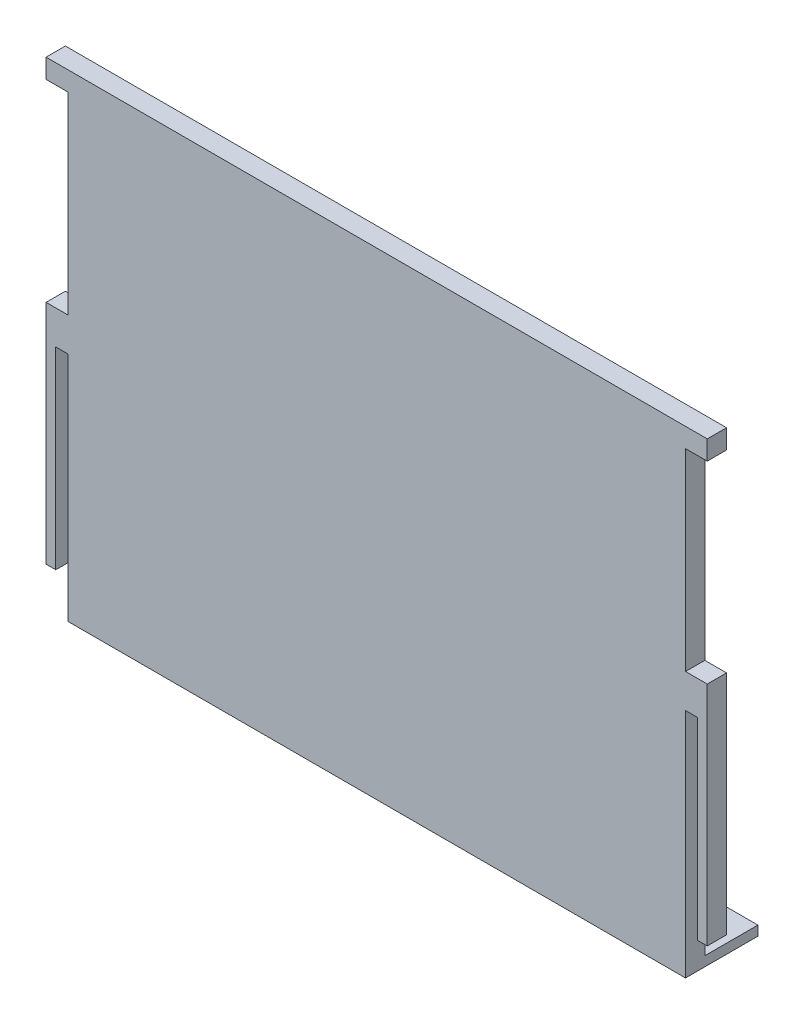
SolidWorks part; units mm, degrees
ref_plane "Front Plane" through (0, 0, 0) normal (0, 0, 1) x (1, 0, 0)
ref_plane "Top Plane" through (0, 0, 0) normal (0, 1, 0) x (1, 0, 0)
ref_plane "Right Plane" through (0, 0, 0) normal (1, 0, 0) x (0, 0, -1)
sketch "Sketch1" plane through (0, 0, 0) normal (0, 0, 1) x (1, 0, 0)
  line L1 (-68.5, -48) -> (68.5, -48)
  line L2 (-68.5, -48) -> (-68.5, 48)
  line L3 (-68.5, 48) -> (68.5, 48)
  line L4 (68.5, -48) -> (68.5, 48)
  line L5 (-68.5, -48) -> (68.5, 48) construction
  line L6 (-68.5, 48) -> (68.5, -48) construction
  point P0 (0, 0)
  dimension "D1" = 137
  dimension "D2" = 96
extrude "Boss-Extrude1" add sketch "Sketch1" along normal blind 4
sketch "Sketch2" plane through (0, 0, 4) normal (0, 0, 1) x (1, 0, 0)
  line L0 (-64, 66.1175) -> (-64, -52.561) construction
  line L1 (64, 66.1175) -> (64, -52.561) construction
  line L2 (-64, -40) -> (-64, 0)
  line L3 (64, 0) -> (64, -40)
  line L4 (-68.5, 48) -> (-68.5, -48) construction
  line L5 (-64, 0) -> (-66.5, 0)
  line L6 (-64, 0) -> (-64, -40)
  line L7 (-64, -40) -> (-66.5, -40)
  line L8 (-66.5, 0) -> (-66.5, -40)
  line L9 (64, 0) -> (66.5, 0)
  line L10 (64, 0) -> (64, -40)
  line L11 (64, -40) -> (66.5, -40)
  line L12 (66.5, 0) -> (66.5, -40)
  line L13 (-68.5, 47) -> (-64, 47)
  line L14 (-68.5, 47) -> (-68.5, 7)
  line L15 (-68.5, 7) -> (-64, 7)
  line L16 (-64, 47) -> (-64, 7)
  line L17 (68.5, -48) -> (68.5, 48) construction
  line L18 (64, 7) -> (68.5, 7)
  line L19 (64, 7) -> (64, 47)
  line L20 (64, 47) -> (68.5, 47)
  line L21 (68.5, 7) -> (68.5, 47)
  dimension "D1" = 128
  dimension "D2" = 64
  dimension "D3" = 40
  dimension "D4" = 2.5
  dimension "D5" = 2.5
  dimension "D6" = 8
  dimension "D7" = 7
  dimension "D8" = 40
extrude "Cut-Extrude1" cut sketch "Sketch2" against normal blind 4 contours L5 L8 L7 L2 | L12 L9 L3 L11 | L14 L15 L16 L13 | L21 L20 L19 L18
sketch "Sketch3" plane through (0, 48, 0) normal (0, 1, 0) x (1, 0, 0)
  line L1 (68.5, -4) -> (-68.5, -4)
  line L2 (68.5, -4) -> (68.5, 0)
  line L3 (68.5, 0) -> (-68.5, 0)
  line L4 (-68.5, -4) -> (-68.5, 0)
extrude "Boss-Extrude2" add sketch "Sketch3" along normal blind 3
sketch "Sketch4" plane through (0, 0, 0) normal (0, 0, -1) x (-1, 0, 0)
  line L0 (68.5, 7) -> (68.5, -48) construction
  line L1 (-68.5, -48) -> (68.5, -48)
  line L2 (-68.5, -48) -> (-68.5, -46)
  line L3 (-68.5, -46) -> (68.5, -46)
  line L4 (68.5, -48) -> (68.5, -46)
  dimension "D1" = 2
extrude "Boss-Extrude3" add sketch "Sketch4" along normal blind 11
sketch "Sketch5" plane through (0, 0, 4) normal (0, 0, 1) x (1, 0, 0)
  line L1 (-64, -40) -> (-68.5, -40)
  line L2 (-64, -40) -> (-64, -48)
  line L3 (-64, -48) -> (-68.5, -48)
  line L4 (-68.5, -40) -> (-68.5, -48)
  line L5 (64, -40) -> (68.5, -40)
  line L6 (64, -40) -> (64, -48)
  line L7 (64, -48) -> (68.5, -48)
  line L8 (68.5, -40) -> (68.5, -48)
extrude "Cut-Extrude2" cut sketch "Sketch5" against normal through all
sketch "Sketch6" plane through (0, 0, 0) normal (0, 0, -1) x (-1, 0, 0)
  line L0 (-20.8, -44.3) -> (-60, -44.3)
  line L1 (60, -44.3) -> (20.8, -44.3)
  line L2 (60, -44.3) -> (60, -16.1)
  line L3 (60, -16.1) -> (20.8, -16.1)
  line L4 (20.8, -44.3) -> (20.8, -16.1)
  line L5 (-20.8, -44.3) -> (-20.8, -16.1)
  line L6 (-20.8, -16.1) -> (-60, -16.1)
  line L7 (-60, -44.3) -> (-60, -16.1)
  line L8 (64, -46) -> (64, 0) construction
  line L9 (-64, 0) -> (-64, -46) construction
  line L10 (-64, -48) -> (64, -48) construction
  line L11 (64, 47) -> (64, 7) construction
  line L12 (34.6, -9.3) -> (-34.6, -9.3)
  line L13 (34.6, -9.3) -> (34.6, 44.9)
  line L14 (34.6, 44.9) -> (-34.6, 44.9)
  line L15 (-34.6, -9.3) -> (-34.6, 44.9)
  dimension "D1" = 39.2
  dimension "D2" = 28.2
  dimension "D3" = 4
  dimension "D4" = 4
  dimension "D5" = 3.7
  dimension "D6" = 69.2
  dimension "D7" = 54.2
  dimension "D8" = 29.4
  dimension "D9" = 6.8
extrude "Cut-Extrude3" cut sketch "Sketch6" against normal blind 2
